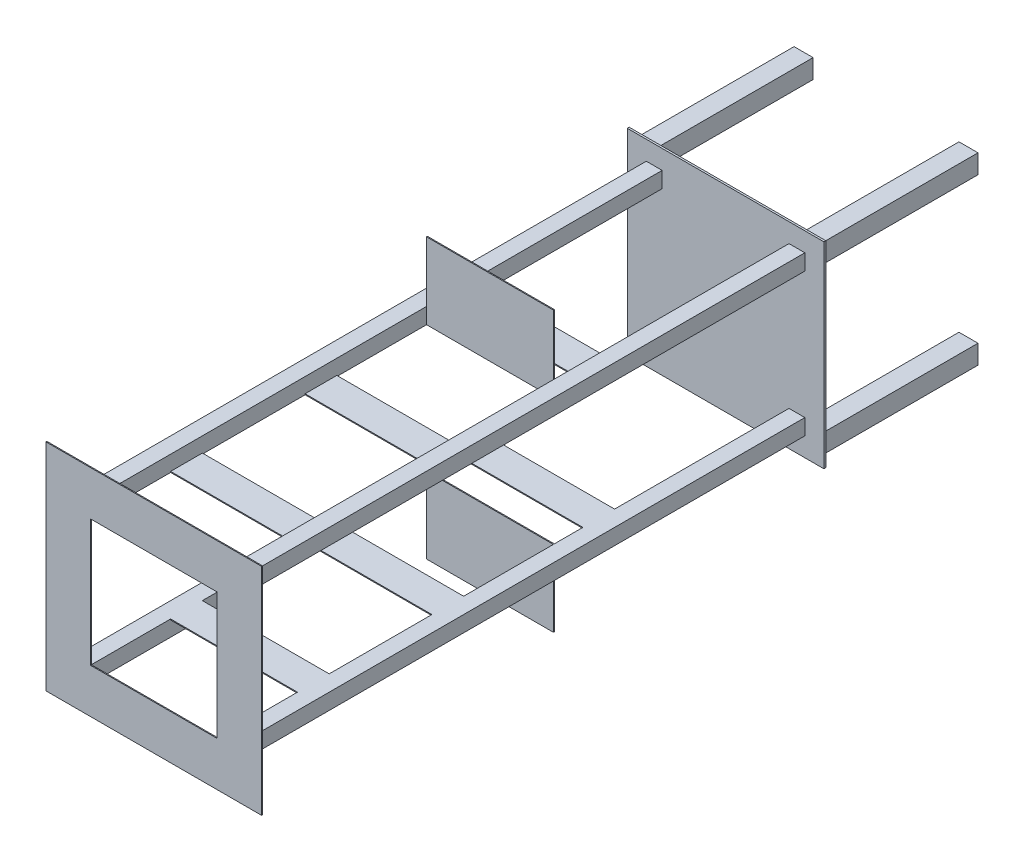
SolidWorks part; units mm, degrees
ref_plane "前基準面" through (0, 0, 0) normal (0, 0, 1) x (1, 0, 0)
ref_plane "上基準面" through (0, 0, 0) normal (0, 1, 0) x (1, 0, 0)
ref_plane "右基準面" through (0, 0, 0) normal (1, 0, 0) x (0, 0, -1)
sketch "草圖1" plane through (0, 0, 0) normal (0, 0, 1) x (1, 0, 0)
  line L0 (-96.0687, 115.7874) -> (-70.0687, 115.7874)
  line L1 (-98.0687, 117.7874) -> (-68.0687, 117.7874)
  line L2 (-98.0687, 117.7874) -> (-98.0687, 87.7874)
  line L3 (-98.0687, 87.7874) -> (-68.0687, 87.7874)
  line L4 (-68.0687, 117.7874) -> (-68.0687, 87.7874)
  line L5 (-70.0687, 115.7874) -> (-70.0687, 89.7874)
  line L6 (-96.0687, 89.7874) -> (-70.0687, 89.7874)
  line L7 (-96.0687, 115.7874) -> (-96.0687, 89.7874)
  line L8 (163.9313, 115.7874) -> (189.9313, 115.7874)
  line L9 (161.9313, 117.7874) -> (191.9313, 117.7874)
  line L10 (161.9313, 117.7874) -> (161.9313, 87.7874)
  line L11 (161.9313, 87.7874) -> (191.9313, 87.7874)
  line L12 (191.9313, 117.7874) -> (191.9313, 87.7874)
  line L13 (189.9313, 115.7874) -> (189.9313, 89.7874)
  line L14 (163.9313, 89.7874) -> (189.9313, 89.7874)
  line L15 (163.9313, 115.7874) -> (163.9313, 89.7874)
  line L16 (163.9313, -144.2126) -> (189.9313, -144.2126)
  line L17 (-98.0687, -142.2126) -> (-68.0687, -142.2126)
  line L18 (-98.0687, -142.2126) -> (-98.0687, -172.2126)
  line L19 (-98.0687, -172.2126) -> (-68.0687, -172.2126)
  line L20 (-68.0687, -142.2126) -> (-68.0687, -172.2126)
  line L21 (161.9313, -142.2126) -> (191.9313, -142.2126)
  line L22 (161.9313, -142.2126) -> (161.9313, -172.2126)
  line L23 (161.9313, -172.2126) -> (191.9313, -172.2126)
  line L24 (191.9313, -142.2126) -> (191.9313, -172.2126)
  line L25 (189.9313, -144.2126) -> (189.9313, -170.2126)
  line L26 (163.9313, -170.2126) -> (189.9313, -170.2126)
  line L27 (163.9313, -144.2126) -> (163.9313, -170.2126)
  line L28 (-96.0687, -144.2126) -> (-70.0687, -144.2126)
  line L29 (-70.0687, -144.2126) -> (-70.0687, -170.2126)
  line L30 (-96.0687, -170.2126) -> (-70.0687, -170.2126)
  line L31 (-96.0687, -144.2126) -> (-96.0687, -170.2126)
  point P32 (161.9313, -157.2126)
  dimension "D1" = 30
  dimension "D2" = 30
  dimension "D4" = 30
  dimension "D5" = 30
  dimension "D7" = 230
  dimension "D8" = 30
  dimension "D9" = 30
  dimension "D10" = 30
  dimension "30" = 30
  dimension "D13" = 230
  dimension "D14" = 230
  dimension "D15" = 230
  dimension "D16" = 0
  dimension "D3" = 2
  dimension "D6" = 2
  dimension "D11" = 2
  dimension "D12" = 2
extrude "填料-伸長1" add sketch "草圖1" along normal blind 250 contours L11 L12 L9 L10 | L14 L13 L8 L15 | L23 L24 L21 L22 | L6 L5 L0 L7 | L3 L4 L1 L2 | L25 L26 L27 L16 | L17 L20 L19 L18 | L28 L29 L30 L31
sketch "草圖2" plane through (0, 0, 250) normal (0, 0, 1) x (1, 0, 0)
  line L0 (-98.0687, 117.7874) -> (-98.0687, 87.7874) construction
  line L1 (-108.0687, 127.7874) -> (201.9313, 127.7874)
  line L2 (-108.0687, 127.7874) -> (-108.0687, -182.2126)
  line L3 (-108.0687, -182.2126) -> (201.9313, -182.2126)
  line L4 (201.9313, 127.7874) -> (201.9313, -182.2126)
  line L5 (-98.0687, 117.7874) -> (-68.0687, 117.7874) construction
  line L6 (191.9313, -142.2126) -> (191.9313, -172.2126) construction
  line L7 (161.9313, -172.2126) -> (191.9313, -172.2126) construction
  dimension "D1" = 10
  dimension "D2" = 10
  dimension "D3" = 10
  dimension "D4" = 10
extrude "填料-伸長2" add sketch "草圖2" along normal blind 3
sketch "草圖5" plane through (0, 0, 253) normal (0, 0, 1) x (1, 0, 0)
  line L0 (-76.5687, 96.2874) -> (-54.5687, 96.2874)
  line L1 (-78.0687, 97.7874) -> (-53.0687, 97.7874)
  line L2 (-78.0687, 97.7874) -> (-78.0687, 72.7874)
  line L3 (-78.0687, 72.7874) -> (-53.0687, 72.7874)
  line L4 (-53.0687, 97.7874) -> (-53.0687, 72.7874)
  line L5 (-54.5687, 96.2874) -> (-54.5687, 74.2874)
  line L6 (-76.5687, 74.2874) -> (-54.5687, 74.2874)
  line L7 (-76.5687, 96.2874) -> (-76.5687, 74.2874)
  line L8 (-76.5687, -128.7126) -> (-54.5687, -128.7126)
  line L9 (-78.0687, -127.2126) -> (-53.0687, -127.2126)
  line L10 (-78.0687, -127.2126) -> (-78.0687, -152.2126)
  line L11 (-78.0687, -152.2126) -> (-53.0687, -152.2126)
  line L12 (-53.0687, -127.2126) -> (-53.0687, -152.2126)
  line L13 (-54.5687, -128.7126) -> (-54.5687, -150.7126)
  line L14 (-76.5687, -150.7126) -> (-54.5687, -150.7126)
  line L15 (-76.5687, -128.7126) -> (-76.5687, -150.7126)
  line L16 (-108.0687, -182.2126) -> (201.9313, -182.2126) construction
  line L17 (-108.0687, 127.7874) -> (-108.0687, -182.2126) construction
  line L18 (46.9313, 127.7874) -> (46.9313, -191.9182) construction
  line L19 (201.9313, 127.7874) -> (-108.0687, 127.7874) construction
  line L20 (170.4313, -128.7126) -> (170.4313, -150.7126)
  line L21 (170.4313, -150.7126) -> (148.4313, -150.7126)
  line L22 (148.4313, -128.7126) -> (148.4313, -150.7126)
  line L23 (146.9313, -127.2126) -> (146.9313, -152.2126)
  line L24 (171.9313, -152.2126) -> (146.9313, -152.2126)
  line L25 (171.9313, -127.2126) -> (171.9313, -152.2126)
  line L26 (171.9313, -127.2126) -> (146.9313, -127.2126)
  line L27 (170.4313, -128.7126) -> (148.4313, -128.7126)
  line L28 (170.4313, 96.2874) -> (170.4313, 74.2874)
  line L29 (170.4313, 74.2874) -> (148.4313, 74.2874)
  line L30 (148.4313, 96.2874) -> (148.4313, 74.2874)
  line L31 (146.9313, 97.7874) -> (146.9313, 72.7874)
  line L32 (171.9313, 72.7874) -> (146.9313, 72.7874)
  line L33 (171.9313, 97.7874) -> (171.9313, 72.7874)
  line L34 (171.9313, 97.7874) -> (146.9313, 97.7874)
  line L35 (170.4313, 96.2874) -> (148.4313, 96.2874)
  dimension "D1" = 25
  dimension "D2" = 25
  dimension "D4" = 25
  dimension "D5" = 25
  dimension "D7" = 250
  dimension "D8" = 30
  dimension "D9" = 30
  dimension "D10" = 30
  dimension "D3" = 1.5
  dimension "D6" = 1.5
extrude "填料-伸長3" add sketch "草圖5" along normal blind 900 contours L4 L1 L2 L3 L7 L0 L5 L6 | L13 L14 L15 L8 | L12 L11 L10 L9 | L20 L21 L22 L27 | L25 L24 L23 L26 | L28 L29 L30 L35 | L33 L32 L31 L34
sketch "草圖6" plane through (0, 0, 1153) normal (0, 0, 1) x (1, 0, 0)
  line L1 (-123.0687, 142.7874) -> (216.9313, 142.7874)
  line L2 (-123.0687, 142.7874) -> (-123.0687, -197.2126)
  line L3 (-123.0687, -197.2126) -> (216.9313, -197.2126)
  line L4 (216.9313, 142.7874) -> (216.9313, -197.2126)
  line L5 (-53.0687, 72.7874) -> (146.9313, 72.7874)
  line L6 (-53.0687, 72.7874) -> (-53.0687, -127.2126)
  line L7 (-53.0687, -127.2126) -> (146.9313, -127.2126)
  line L8 (146.9313, 72.7874) -> (146.9313, -127.2126)
  dimension "D2" = 70
  dimension "D3" = 70
  dimension "D4" = 70
  dimension "70" = 70
extrude "填料-伸長4" add sketch "草圖6" along normal blind 1.5
ref_plane "平面1" through (0, 0, 623) normal (0, 0, 1) x (1, 0, 0)
sketch "草圖7" plane through (0, 0, 623) normal (0, 0, 1) x (1, 0, 0)
  line L1 (-53.0687, 72.7874) -> (146.9313, 72.7874)
  line L2 (-53.0687, 72.7874) -> (-53.0687, 192.7874)
  line L3 (-53.0687, 192.7874) -> (146.9313, 192.7874)
  line L4 (146.9313, 72.7874) -> (146.9313, 192.7874)
  line L6 (146.9313, -127.2126) -> (-53.0687, -127.2126)
  line L7 (146.9313, -127.2126) -> (146.9313, -247.2126)
  line L8 (146.9313, -247.2126) -> (-53.0687, -247.2126)
  line L9 (-53.0687, -127.2126) -> (-53.0687, -247.2126)
  line L10 (-53.0687, 72.7874) -> (-53.0687, -127.2126) construction
  line L13 (146.9313, -127.2126) -> (146.9313, 72.7874) construction
  line L14 (-53.0687, -127.2126) -> (146.9313, -127.2126) construction
  dimension "D1" = 0
  dimension "D2" = 0
  dimension "D3" = 0
  dimension "D4" = 0
  dimension "D5" = 0
  dimension "D6" = 120
  dimension "D7" = 120
extrude "填料-伸長5" add sketch "草圖7" along normal blind 1.5
ref_plane "平面2" through (0, 0, 1003) normal (0, 0, -1) x (-1, 0, 0)
ref_plane "平面3" through (0, 0, 553) normal (0, 0, -1) x (-1, 0, 0)
ref_plane "平面5" through (0, 0, 791) normal (0, 0, -1) x (-1, 0, 0)
sketch "草圖8" plane through (0, 0, 1003) normal (0, 0, -1) x (-1, 0, 0)
  line L0 (-146.9313, 72.7874) -> (53.0687, 72.7874) construction
  line L1 (-146.9313, 72.7874) -> (53.0687, 72.7874)
  line L2 (-146.9313, 72.7874) -> (-146.9313, 74.2874)
  line L3 (-146.9313, 74.2874) -> (53.0687, 74.2874)
  line L4 (53.0687, 72.7874) -> (53.0687, 74.2874)
  line L6 (-146.9313, -127.2126) -> (53.0687, -127.2126)
  line L7 (-146.9313, -127.2126) -> (-146.9313, -128.7126)
  line L8 (-146.9313, -128.7126) -> (53.0687, -128.7126)
  line L9 (53.0687, -127.2126) -> (53.0687, -128.7126)
  line L11 (53.0687, -127.2126) -> (-146.9313, -127.2126) construction
  line L12 (53.0687, 72.7874) -> (53.0687, -127.2126) construction
  line L13 (-146.9313, -127.2126) -> (-146.9313, 72.7874) construction
  dimension "D1" = 1.5
  dimension "D2" = 1.5
  dimension "D3" = 0
  dimension "D4" = 0
  dimension "D5" = 0
  dimension "D6" = 0
  dimension "D7" = 0
  dimension "D8" = 0
extrude "填料-伸長6" add sketch "草圖8" along normal mid plane 50
sketch "草圖9" plane through (0, 0, 791) normal (0, 0, -1) x (-1, 0, 0)
  line L1 (53.0687, 72.7874) -> (-146.9313, 72.7874)
  line L2 (53.0687, 72.7874) -> (53.0687, 74.2874)
  line L3 (53.0687, 74.2874) -> (-146.9313, 74.2874)
  line L4 (-146.9313, 72.7874) -> (-146.9313, 74.2874)
  line L5 (53.0687, -127.2126) -> (-146.9313, -127.2126)
  line L6 (53.0687, -127.2126) -> (53.0687, -128.7126)
  line L7 (53.0687, -128.7126) -> (-146.9313, -128.7126)
  line L8 (-146.9313, -127.2126) -> (-146.9313, -128.7126)
  dimension "D1" = 1.5
  dimension "D2" = 1.5
extrude "填料-伸長7" add sketch "草圖9" along normal mid plane 50
sketch "草圖11" plane through (0, 0, 553) normal (0, 0, -1) x (-1, 0, 0)
  line L1 (53.0687, -127.2126) -> (-146.9313, -127.2126)
  line L2 (53.0687, -127.2126) -> (53.0687, -128.7126)
  line L3 (53.0687, -128.7126) -> (-146.9313, -128.7126)
  line L4 (-146.9313, -127.2126) -> (-146.9313, -128.7126)
  line L5 (53.0687, 72.7874) -> (-146.9313, 72.7874)
  line L6 (53.0687, 72.7874) -> (53.0687, 74.2874)
  line L7 (53.0687, 74.2874) -> (-146.9313, 74.2874)
  line L8 (-146.9313, 72.7874) -> (-146.9313, 74.2874)
  dimension "D1" = 1.5
  dimension "D2" = 1.5
extrude "填料-伸長8" add sketch "草圖11" along normal mid plane 50
